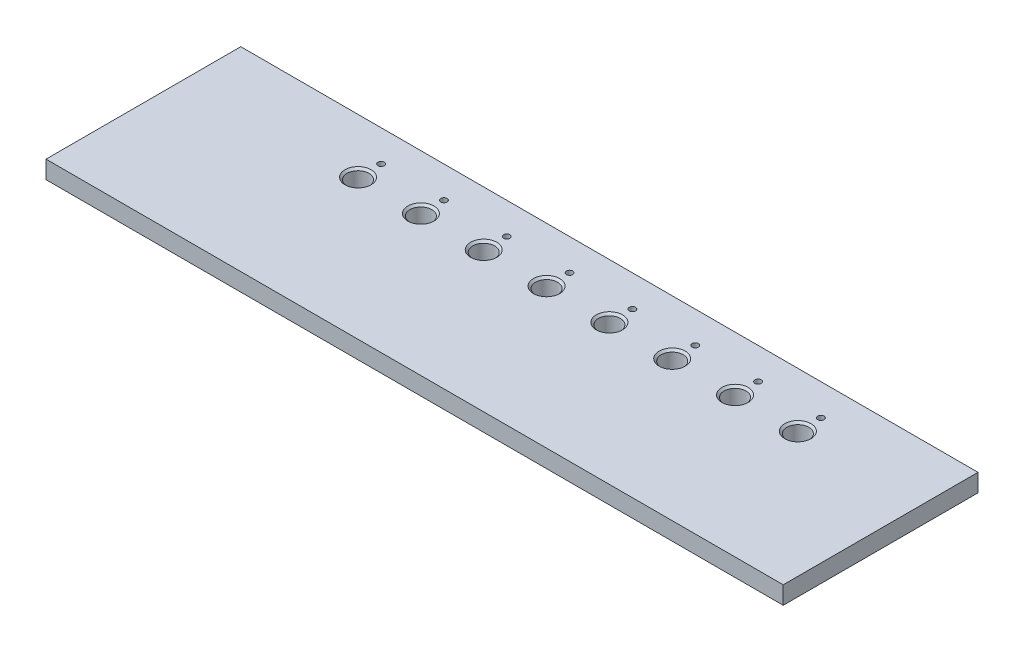
SolidWorks part; units mm, degrees
material "Chêne"
ref_plane "Plan de face" through (0, 0, 0) normal (0, 0, 1) x (1, 0, 0)
ref_plane "Plan de dessus" through (0, 0, 0) normal (0, 1, 0) x (1, 0, 0)
ref_plane "Plan de droite" through (0, 0, 0) normal (1, 0, 0) x (0, 0, -1)
sketch "Esquisse5" plane through (0, 0, 0) normal (0, 1, 0) x (1, 0, 0)
  line L1 (181, 0) -> (-171, 0)
  line L2 (181, 0) -> (181, -93)
  line L3 (181, -93) -> (-171, -93)
  line L4 (-171, 0) -> (-171, -93)
  dimension "D1" = 93
  dimension "D2" = 10
extrude "Boss.-Extru.2" add sketch "Esquisse5" against normal up to vertex (8.5 mm away)
sketch "Esquisse3" plane through (0, 0, 0) normal (0, 1, 0) x (1, 0, 0)
  line L0 (-89, -15) -> (-59, -15) construction
  line L2 (-181, 0) -> (181, 0) construction
  circle A0 centre (-89, -15) radius 1.5
  circle A1 centre (-89, -26) radius 5.25
  circle A3 centre (-59, -15) radius 1.5
  circle A4 centre (-59, -26) radius 5.25
  circle A5 centre (-29, -15) radius 1.5
  circle A6 centre (-29, -26) radius 5.25
  circle A7 centre (1, -15) radius 1.5
  circle A8 centre (1, -26) radius 5.25
  circle A9 centre (31, -15) radius 1.5
  circle A10 centre (31, -26) radius 5.25
  circle A11 centre (61, -15) radius 1.5
  circle A12 centre (61, -26) radius 5.25
  circle A13 centre (91, -15) radius 1.5
  circle A14 centre (91, -26) radius 5.25
  circle A15 centre (121, -15) radius 1.5
  circle A16 centre (121, -26) radius 5.25
  circle A19 centre (-89, 15) radius 9.5 construction
  dimension "D1" = 3
  dimension "D2" = 10.5
  dimension "D7" = 0
  dimension "D3" = 11
  dimension "D5" = 30
  dimension "D6" = 15
  dimension "D4" = 8
extrude "Enlèv. mat.-Extru.1" cut sketch "Esquisse3" against normal through all
chamfer "Chanfrein1" distance 1 angle 45 8 edges at (121, 0, 31.25) (91, 0, 31.25) (61, 0, 31.25) (31, 0, 31.25) (1, 0, 31.25) (-29, 0, 31.25) (-59, 0, 31.25) (-89, 0, 31.25)
